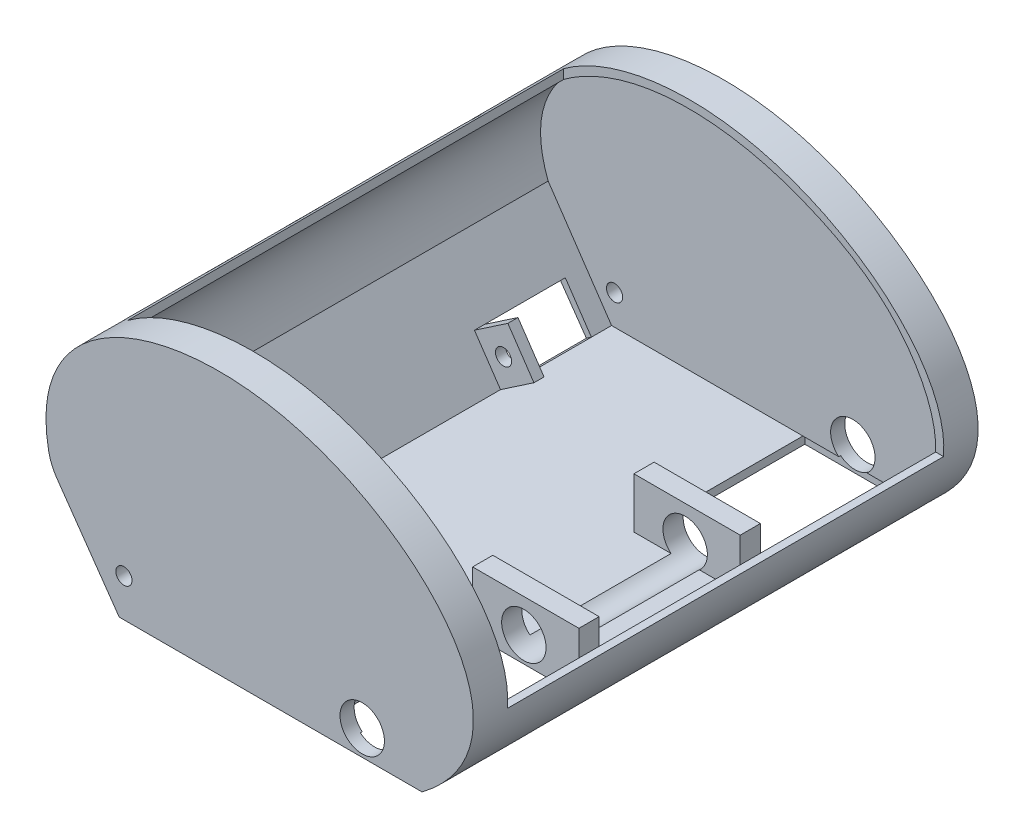
SolidWorks part; units mm, degrees
ref_plane "Front Plane" through (0, 0, 0) normal (0, 0, 1) x (1, 0, 0)
ref_plane "Top Plane" through (0, 0, 0) normal (0, 1, 0) x (1, 0, 0)
ref_plane "Right Plane" through (0, 0, 0) normal (1, 0, 0) x (0, 0, -1)
sketch "Sketch1" plane through (0, 0, 0) normal (0, 0, 1) x (1, 0, 0)
  line L0 (-74.4669, 0) -> (75.5331, 0)
  line L1 (-108.0812, 48.036) -> (-74.4669, 0)
  spline S0 degree 3 poles (75.5331, 0) (138.0634, 47.2005) (16.47, 172.0078) (-124.9496, 111.3016) (-108.0812, 48.036) knots 0 0 0 0 0.526875 1 1 1 1
  point P4 (-32.4145, 130)
  dimension "D1" = 150
  dimension "D2" = 130
extrude "Boss-Extrude1" add sketch "Sketch1" along normal blind 250
sketch "Sketch2" plane through (0, 0, 250) normal (0, 0, 1) x (1, 0, 0)
  line L0 (-105.0026, 50.2782) -> (-73.6035, 4)
  line L1 (-73.6035, 4) -> (73.1634, 4)
  line L2 (-74.4669, 0) -> (75.5331, 0) construction
  line L3 (-108.0812, 48.036) -> (-74.4669, 0) construction
  line L4 (73.1634, 4) -> (80.7933, 10.7284)
  spline S1 degree 3 poles (80.7933, 10.7284) (92.6518, 19.5638) (103.0098, 45.2056) (79.954, 88.9181) (40.6079, 112.9561) (-11.2048, 129.1427) (-79.4317, 124.6676) (-117.3447, 82.3238) (-105.0026, 50.2782) knots 0.016279 0.016279 0.016279 0.016279 0.126753 0.268313 0.414747 0.542883 0.761533 1 1 1 1
  spline S2 degree 3 poles (75.5331, 0) (138.0634, 47.2005) (16.47, 172.0078) (-124.9496, 111.3016) (-108.0812, 48.036) knots 0 0 0 0 0.526875 1 1 1 1 construction
  point P14 (40.9507, 114.8274)
  point P15 (100.9403, 42.4125)
  point P16 (-27.9262, 130.1717)
  point P17 (-96.6085, 104.0044)
  point P18 (-110.7265, 67.1672)
  point P19 (-108.4645, 63.8682)
  point P20 (-106.6025, 82.7288)
  point P21 (-109.6025, 78.5997)
  point P24 (-89.3031, 27.1391)
  dimension "D5" = 4
  dimension "D1" = 4
  dimension "D2" = 4
  dimension "D3" = 4
  dimension "D4" = 6
  dimension "D6" = 3
  dimension "D7" = 3.4043
extrude "Cut-Extrude1" cut sketch "Sketch2" against normal blind 236 from offset 7 offset against normal yes
sketch "Sketch3" plane through (0, 0, 0) normal (0, 1, 0) x (1, 0, 0)
  line L0 (-87.293, -17) -> (-87.293, -233)
  line L1 (-87.293, -233) -> (100.952, -233)
  line L2 (100.952, -250) -> (100.952, 0) construction
  line L3 (100.952, -233) -> (100.952, -17)
  line L4 (100.952, -17) -> (-87.293, -17)
  line L5 (100.952, 0) -> (-110.7265, 0) construction
  line L6 (-110.7265, -250) -> (100.952, -250) construction
  dimension "D1" = 17
  dimension "D2" = 17
extrude "Cut-Extrude2" cut sketch "Sketch3" along normal blind 236 from offset 40
fillet "Fillet1" radius 25 1 edges at (-108.0812, 48.036, 125)
sketch "Sketch16" plane through (-48.5432, -32.9358, 0) normal (0.8275, 0.5615, 0) x (0, 0, -1)
  line L0 (-7, 44.6349) -> (-243, 44.6349) construction
  line L1 (-232.3287, 45.426) -> (-192.3287, 45.426)
  line L2 (-232.3287, 45.426) -> (-232.3287, 68.426)
  line L3 (-232.3287, 68.426) -> (-192.3287, 68.426)
  line L4 (-192.3287, 45.426) -> (-192.3287, 68.426)
  line L5 (-17, 44.6349) -> (-57, 44.6349)
  line L6 (-17, 44.6349) -> (-17, 67.6349)
  line L7 (-17, 67.6349) -> (-57, 67.6349)
  line L8 (-57, 44.6349) -> (-57, 67.6349)
  line L10 (-17, 142.0334) -> (-17, -23.504) construction
  point P10 (-237.1387, 68.3072)
  point P11 (-45.8804, 67.6349)
  point P12 (0, 0)
  point P13 (-37.3571, 67.6349)
  point P14 (0, 0)
  point P15 (0, 0)
  point P16 (0, 0)
  point P17 (0, 0)
  point P18 (0, 0)
  point P19 (-212.5355, 68.5749)
  point P20 (-182.3287, 68.426)
  point P21 (-66.95, 67.6349)
  point P22 (0, 0)
  point P23 (0, 0)
  point P24 (-17, 67.6349)
  dimension "D1" = 23
  dimension "D2" = 40
  dimension "D3" = 23
  dimension "D4" = 40
extrude "Cut-Extrude11" cut sketch "Sketch16" against normal blind 170
sketch "Sketch17" plane through (-48.5432, -32.9358, 0) normal (0.8275, 0.5615, 0) x (0, 0, -1)
  line L0 (-57, 44.6349) -> (-243, 44.6349) construction
  line L1 (-192.3287, 68.426) -> (-187.3287, 68.426)
  line L2 (-192.3287, 68.426) -> (-192.3287, 44.6349)
  line L3 (-192.3287, 44.6349) -> (-187.3287, 44.6349)
  line L4 (-187.3287, 68.426) -> (-187.3287, 44.6349)
  line L7 (-57, 67.6349) -> (-62, 67.6349)
  line L8 (-57, 67.6349) -> (-57, 44.6349)
  line L9 (-57, 44.6349) -> (-62, 44.6349)
  line L10 (-62, 67.6349) -> (-62, 44.6349)
  dimension "D1" = 5
  dimension "D2" = 5
extrude "Boss-Extrude5" add sketch "Sketch17" along normal blind 20
sketch "Sketch18" plane through (0, 0, 57) normal (0, 0, -1) x (-1, 0, 0)
  circle A0 centre (72.1247, 18.8437) radius 4
  dimension "D1" = 8
extrude "Cut-Extrude12" cut sketch "Sketch18" against normal through all both and the other way through all
sketch "Sketch21" plane through (0, 4, 0) normal (0, 1, 0) x (1, 0, 0)
  line L0 (73.1634, -7) -> (73.1634, -243) construction
  line L1 (73.1634, -243.9444) -> (21.1634, -243.9444)
  line L2 (73.1634, -243.9444) -> (73.1634, -169.9444)
  line L3 (73.1634, -169.9444) -> (21.1634, -169.9444)
  line L4 (21.1634, -243.9444) -> (21.1634, -169.9444)
  dimension "D1" = 74
  dimension "D2" = 52
extrude "Cut-Extrude13" cut sketch "Sketch21" against normal blind 10
sketch "Sketch22" plane through (0, 4, 0) normal (0, 1, 0) x (1, 0, 0)
  line L1 (73.1634, -169.9444) -> (20.5248, -169.9444)
  line L2 (73.1634, -169.9444) -> (73.1634, -159.9444)
  line L3 (73.1634, -159.9444) -> (20.5248, -159.9444)
  line L4 (20.5248, -169.9444) -> (20.5248, -159.9444)
  dimension "D1" = 10
extrude "Boss-Extrude6" add sketch "Sketch22" along normal blind 25
ref_plane "Plane1" through (0, 0, 125) normal (0, 0, 1) x (1, 0, 0)
mirror "Mirror2" about plane through (0, 0, 125) normal (0, 0, 1) of "Boss-Extrude6", "Cut-Extrude13"
sketch "Sketch24" plane through (0, 0, 169.9444) normal (0, 0, 1) x (1, 0, 0)
  line L0 (-74.4669, 0) -> (75.5331, 0) construction
  line L1 (71.8906, 0) -> (19.8906, 0) construction
  line L2 (71.8906, 0) -> (71.8906, 25) construction
  line L3 (71.8906, 25) -> (19.8906, 25) construction
  line L4 (19.8906, 0) -> (19.8906, 25) construction
  circle A0 centre (45.8906, 12.5) radius 11
  dimension "D3" = 22
  dimension "D1" = 52
  dimension "D2" = 25
  dimension "D4" = 12.5
  dimension "D5" = 26
extrude "Cut-Extrude14" cut sketch "Sketch24" against normal through all both and the other way through all
